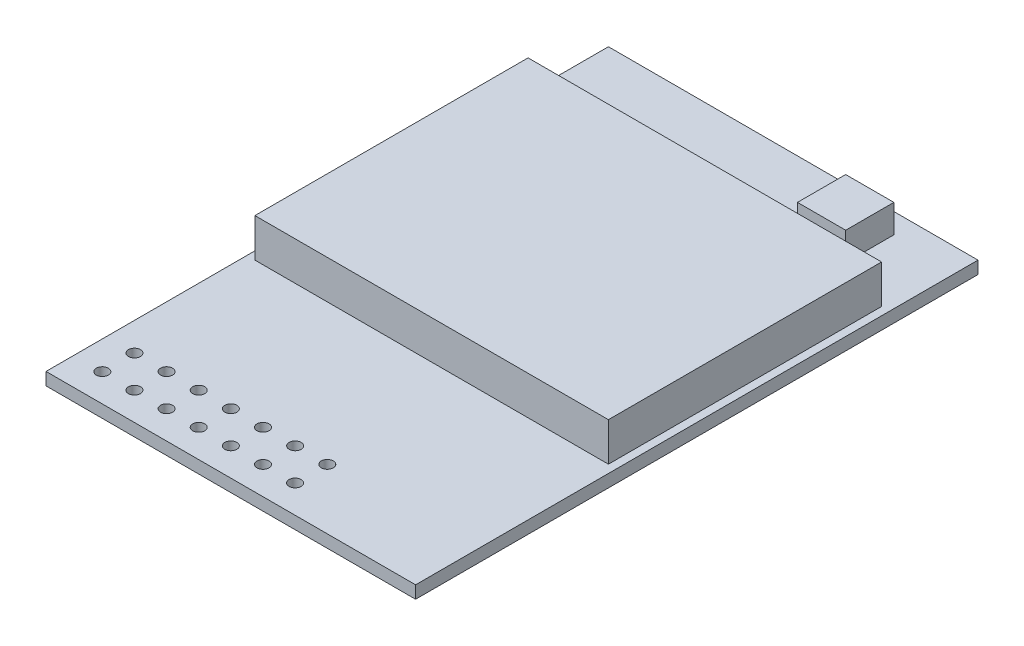
SolidWorks part; units mm, degrees
ref_plane "Front Plane" through (0, 0, 0) normal (0, 0, 1) x (1, 0, 0)
ref_plane "Top Plane" through (0, 0, 0) normal (0, 1, 0) x (1, 0, 0)
ref_plane "Right Plane" through (0, 0, 0) normal (1, 0, 0) x (0, 0, -1)
sketch "Sketch1" plane through (0, 0, 0) normal (0, 1, 0) x (1, 0, 0)
  line L1 (-11.5, -17.5) -> (11.5, -17.5)
  line L2 (-11.5, -17.5) -> (-11.5, 17.5)
  line L3 (-11.5, 17.5) -> (11.5, 17.5)
  line L4 (11.5, -17.5) -> (11.5, 17.5)
  line L5 (-11.5, -17.5) -> (11.5, 17.5) construction
  line L6 (-11.5, 17.5) -> (11.5, -17.5) construction
  circle A0 centre (0, 0) radius 20.9404 construction
  point P0 (0, 0)
  dimension "D3" = 41.8808
  dimension "D1" = 23
  dimension "D2" = 35
extrude "Boss-Extrude1" add sketch "Sketch1" along normal blind 0.78
sketch "Sketch2" plane through (0, 0.78, 0) normal (0, 1, 0) x (1, 0, 0)
  line L1 (-11, 12) -> (11, 12)
  line L2 (-11, 12) -> (-11, -5)
  line L3 (-11, -5) -> (11, -5)
  line L4 (11, 12) -> (11, -5)
  line L5 (-11, 12) -> (11, -5) construction
  line L6 (-11, -5) -> (11, 12) construction
  point P0 (0, 3.5)
  point P5 (0, 0)
  dimension "D1" = 22
  dimension "D2" = 17
  dimension "D3" = 3.5
extrude "Boss-Extrude2" add sketch "Sketch2" along normal blind 2.4
sketch "Sketch3" plane through (0, 0.78, 0) normal (0, 1, 0) x (1, 0, 0)
  line L1 (4.5213, 16.2441) -> (7.5213, 16.2441)
  line L2 (4.5213, 16.2441) -> (4.5213, 13.2441)
  line L3 (4.5213, 13.2441) -> (7.5213, 13.2441)
  line L4 (7.5213, 16.2441) -> (7.5213, 13.2441)
  line L5 (4.5213, 16.2441) -> (7.5213, 13.2441) construction
  line L6 (4.5213, 13.2441) -> (7.5213, 16.2441) construction
  point P0 (6.0213, 14.7441)
  point P5 (6.0213, 14.7441)
  dimension "D1" = 3
extrude "Boss-Extrude3" add sketch "Sketch3" along normal blind 1.75
sketch "Sketch4" plane through (0, 0.78, 0) normal (0, 1, 0) x (1, 0, 0)
  circle A0 centre (-9.7369, -15.7591) radius 0.375
  circle A1 centre (-7.7369, -15.7591) radius 0.375
  circle A2 centre (-5.7369, -15.7591) radius 0.375
  circle A3 centre (-3.7369, -15.7591) radius 0.375
  circle A4 centre (-1.7369, -15.7591) radius 0.375
  circle A5 centre (0.2631, -15.7591) radius 0.375
  circle A6 centre (2.2631, -15.7591) radius 0.375
  circle A7 centre (-7.7369, -13.7591) radius 0.375
  circle A8 centre (-5.7369, -13.7591) radius 0.375
  circle A9 centre (-3.7369, -13.7591) radius 0.375
  circle A10 centre (-1.7369, -13.7591) radius 0.375
  circle A11 centre (0.2631, -13.7591) radius 0.375
  circle A12 centre (2.2631, -13.7591) radius 0.375
  circle A13 centre (-9.7369, -13.7591) radius 0.375
  point P2 (-9.7369, -15.7591)
  point P3 (0, 0)
  dimension "D1" = 0.75
  dimension "D2" = 7
  dimension "D3" = 2
extrude "Cut-Extrude1" cut sketch "Sketch4" against normal through all
